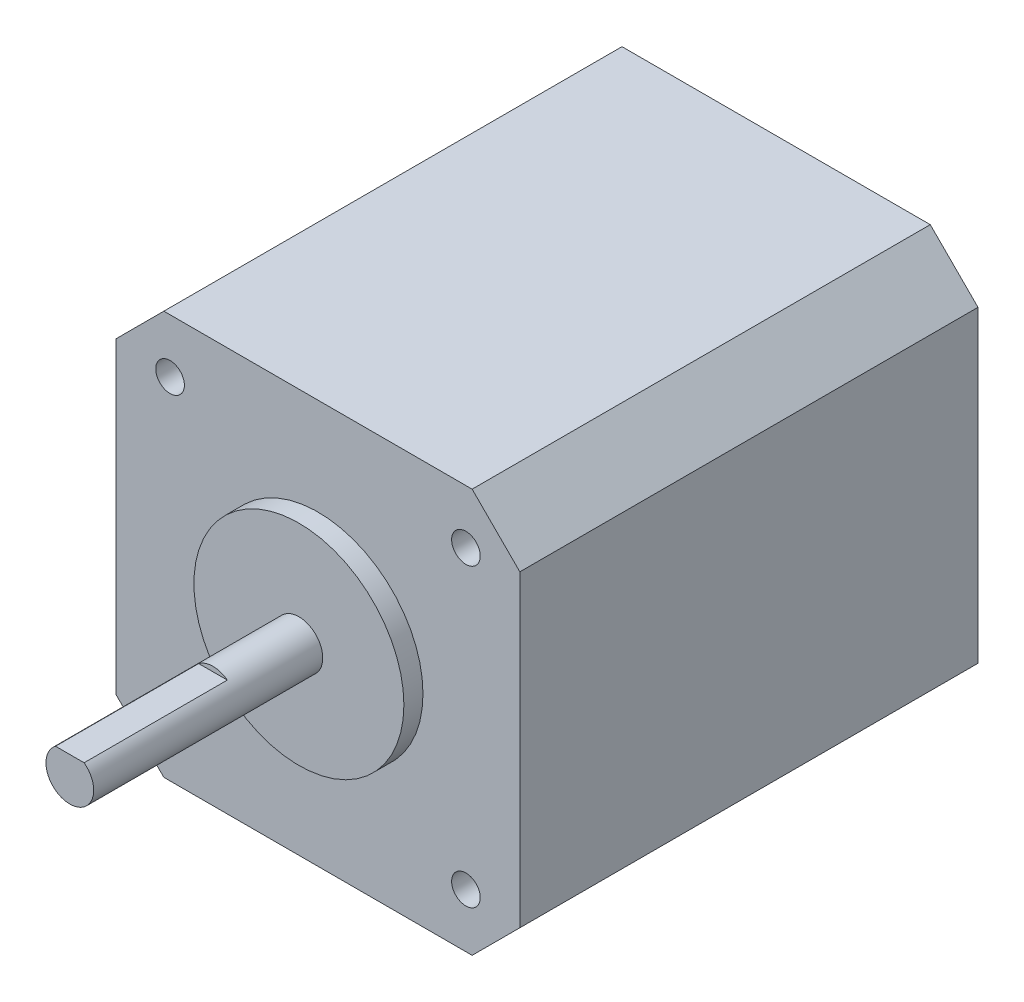
SolidWorks part; units mm, degrees
ref_plane "Front Plane" through (0, 0, 0) normal (0, 0, 1) x (1, 0, 0)
ref_plane "Top Plane" through (0, 0, 0) normal (0, 1, 0) x (1, 0, 0)
ref_plane "Right Plane" through (0, 0, 0) normal (1, 0, 0) x (0, 0, -1)
sketch "Sketch1" plane through (0, 0, 0) normal (0, 0, 1) x (1, 0, 0)
  line L0 (0, 37.3) -> (5, 42.3)
  line L1 (5, 0) -> (37.3, 0)
  line L2 (0, 5) -> (0, 37.3)
  line L3 (5, 42.3) -> (37.3, 42.3)
  line L4 (42.3, 5) -> (42.3, 37.3)
  line L5 (0, 0) -> (42.3, 42.3) construction
  line L6 (0, 42.3) -> (42.3, 0) construction
  line L7 (37.3, 42.3) -> (42.3, 37.3)
  line L8 (37.3, 0) -> (42.3, 5)
  line L9 (0, 5) -> (5, 0)
  circle A0 centre (5.65, 36.65) radius 1.5
  circle A1 centre (36.65, 36.65) radius 1.5
  circle A2 centre (36.65, 5.65) radius 1.5
  circle A3 centre (5.65, 5.65) radius 1.5
  point P4 (21.15, 21.15)
  dimension "D3" = 3
  dimension "D1" = 42.3
  dimension "D2" = 42.3
  dimension "D4" = 31
extrude "Boss-Extrude1" add sketch "Sketch1" along normal blind 48 contours L2 L9 L1 L8 L4 L7 L3 L0 A3 A2 A1 A0
sketch "Sketch2" plane through (0, 0, 48) normal (0, 0, 1) x (1, 0, 0)
  line L0 (21.15, 42.3) -> (21.15, 0) construction
  line L1 (5, 42.3) -> (37.3, 42.3) construction
  line L2 (5, 0) -> (37.3, 0) construction
  line L3 (0, 21.15) -> (42.3, 21.15) construction
  line L4 (0, 5) -> (0, 37.3) construction
  line L5 (42.3, 5) -> (42.3, 37.3) construction
  circle A0 centre (21.15, 21.15) radius 11
  dimension "D1" = 22
extrude "Boss-Extrude2" add sketch "Sketch2" along normal blind 2
sketch "Sketch3" plane through (0, 0, 50) normal (0, 0, 1) x (1, 0, 0)
  circle A0 centre (21.15, 21.15) radius 2.5
  circle A1 centre (21.15, 21.15) radius 11
  circle A2 centre (21.15, 21.15) radius 11 construction
  dimension "D2" = 5
  dimension "D1" = 0
extrude "Boss-Extrude3" add sketch "Sketch3" along normal blind 24 contours A0
sketch "Sketch4" plane through (0, 0, 74) normal (0, 0, 1) x (1, 0, 0)
  line L0 (19.65, 23.15) -> (22.65, 23.15)
  circle A1 centre (21.15, 21.15) radius 2.5
  arc A2 (22.65, 23.15) -> (19.65, 23.15) centre (21.15, 21.15) ccw
  point P1 (21.15, 18.65)
  dimension "D2" = 4.5
  dimension "D1" = 0
extrude "Cut-Extrude1" cut sketch "Sketch4" against normal blind 15
sketch "Sketch5" plane through (0, 0, 0) normal (0, 0, -1) x (-1, 0, 0)
  line L0 (-19.65, 23.15) -> (-22.65, 23.15) construction
  line L1 (-19.65, 23.15) -> (-22.65, 23.15)
  arc A2 (-22.65, 23.15) -> (-19.65, 23.15) centre (-21.15, 21.15) ccw construction
  arc A3 (-22.65, 23.15) -> (-19.65, 23.15) centre (-21.15, 21.15) ccw
extrude "Boss-Extrude5" add sketch "Sketch5" along normal blind 13
